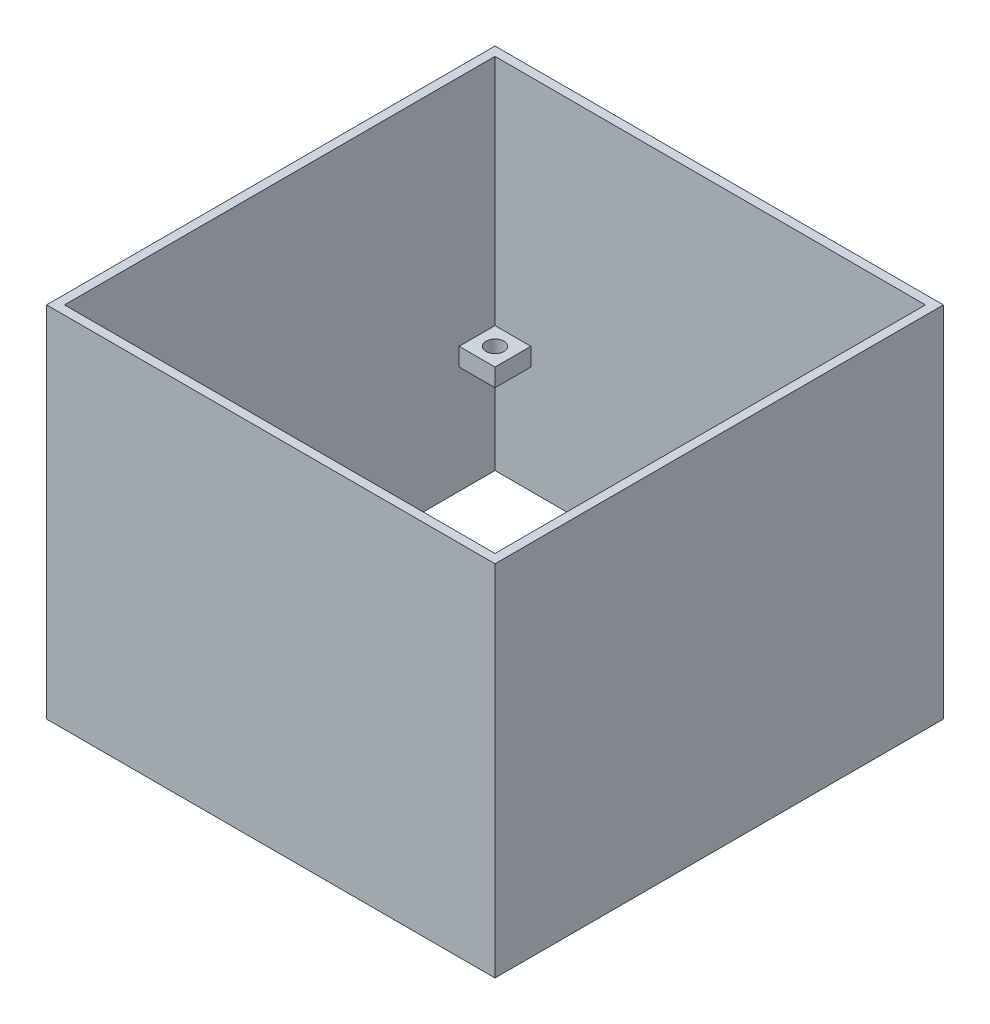
SolidWorks part; units mm, degrees
ref_plane "Front Plane" through (0, 0, 0) normal (0, 0, 1) x (1, 0, 0)
ref_plane "Top Plane" through (0, 0, 0) normal (0, 1, 0) x (1, 0, 0)
ref_plane "Right Plane" through (0, 0, 0) normal (1, 0, 0) x (0, 0, -1)
sketch "Sketch1" plane through (0, 0, 0) normal (0, 1, 0) x (1, 0, 0)
  line L1 (-60, -60) -> (60, -60)
  line L2 (-60, -60) -> (-60, 60)
  line L3 (-60, 60) -> (60, 60)
  line L4 (60, -60) -> (60, 60)
  line L5 (-60, -60) -> (60, 60) construction
  line L6 (-60, 60) -> (60, -60) construction
  line L7 (-62.5, -62.5) -> (62.5, -62.5)
  line L8 (-62.5, -62.5) -> (-62.5, 62.5)
  line L9 (-62.5, 62.5) -> (62.5, 62.5)
  line L10 (62.5, -62.5) -> (62.5, 62.5)
  line L11 (-62.5, -62.5) -> (62.5, 62.5) construction
  line L12 (-62.5, 62.5) -> (62.5, -62.5) construction
  point P0 (0, 0)
  point P6 (0, 0)
  dimension "D1" = 120
  dimension "D2" = 120
  dimension "D3" = 125
  dimension "125" = 125
extrude "Boss-Extrude1" add sketch "Sketch1" along normal blind 100
sketch "Sketch3" plane through (0, 100, 0) normal (0, 1, 0) x (1, 0, 0)
  line L0 (60, 60) -> (50, 60)
  line L1 (-60, 60) -> (-50, 60)
  line L2 (-60, 60) -> (-60, 50)
  line L3 (-60, 50) -> (-50, 50)
  line L4 (-50, 60) -> (-50, 50)
  line L5 (60, 60) -> (60, 50)
  line L6 (60, 50) -> (50, 50)
  line L7 (50, 60) -> (50, 50)
  line L8 (60, -60) -> (60, -50)
  line L9 (60, -60) -> (50, -60)
  line L10 (50, -60) -> (50, -50)
  line L11 (60, -50) -> (50, -50)
  line L12 (-60, -60) -> (-50, -60)
  line L13 (-60, -60) -> (-60, -50)
  line L14 (-60, -50) -> (-50, -50)
  line L15 (-50, -60) -> (-50, -50)
  point P20 (0, 0)
  dimension "D1" = 10
  dimension "D2" = 10
  dimension "D3" = 4
extrude "Boss-Extrude2" add sketch "Sketch3" against normal blind 70
sketch "Sketch4" plane through (0, 30, 0) normal (0, -1, 0) x (1, 0, 0)
  circle A0 centre (-55, 55) radius 2.5
  circle A1 centre (55, 55) radius 2.5
  circle A2 centre (55, -55) radius 2.5
  circle A3 centre (-55, -55) radius 2.5
  point P11 (0, 0)
  dimension "D1" = 5
  dimension "D2" = 4
extrude "Cut-Extrude1" cut sketch "Sketch4" against normal blind 5
sketch "Sketch5" plane through (0, 100, 0) normal (0, 1, 0) x (1, 0, 0)
  line L1 (-60, -60) -> (60, -60)
  line L2 (-60, -60) -> (-60, 60)
  line L3 (-60, 60) -> (60, 60)
  line L4 (60, -60) -> (60, 60)
  line L5 (-60, -60) -> (60, 60) construction
  line L6 (-60, 60) -> (60, -60) construction
  point P0 (0, 0)
extrude "Cut-Extrude2" cut sketch "Sketch5" against normal blind 65
